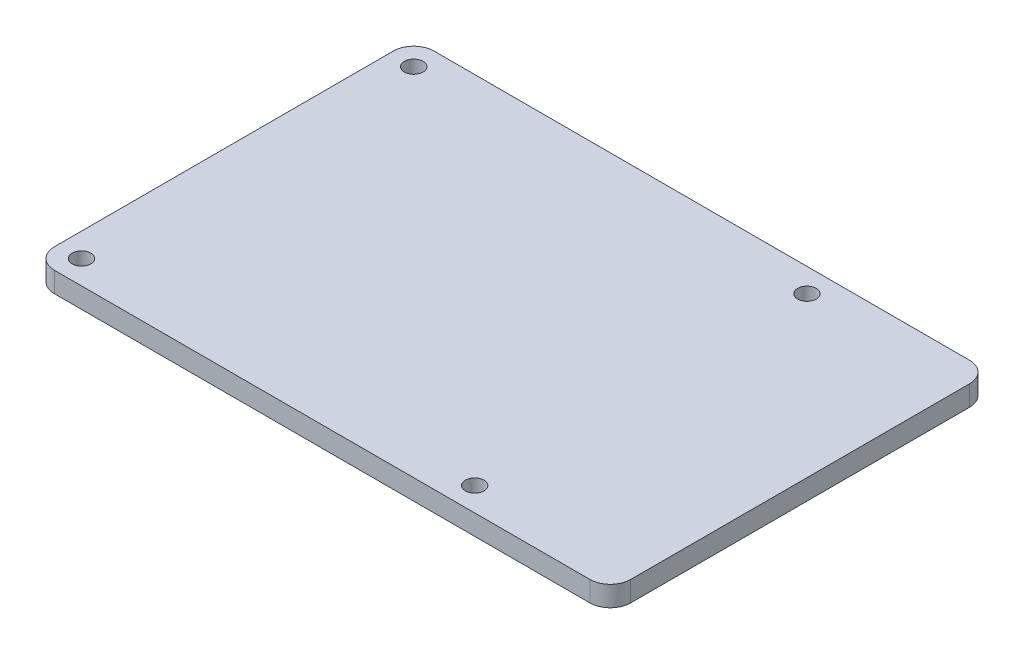
SolidWorks part; units mm, degrees
ref_plane "Front Plane" through (0, 0, 0) normal (0, 0, 1) x (1, 0, 0)
ref_plane "Top Plane" through (0, 0, 0) normal (0, 1, 0) x (1, 0, 0)
ref_plane "Right Plane" through (0, 0, 0) normal (1, 0, 0) x (0, 0, -1)
sketch "Sketch1" plane through (0, 0, 0) normal (0, 1, 0) x (1, 0, 0)
  line L0 (0, 28) -> (85, 28) construction
  line L1 (3, 0) -> (82, 0)
  line L2 (0, 3) -> (0, 53)
  line L3 (3, 56) -> (82, 56)
  line L4 (85, 3) -> (85, 53)
  arc A0 (82, 0) -> (85, 3) centre (82, 3) ccw
  arc A1 (82, 56) -> (85, 53) centre (82, 53) cw
  arc A2 (0, 53) -> (3, 56) centre (3, 53) cw
  arc A3 (3, 0) -> (0, 3) centre (3, 3) cw
  circle A4 centre (3.5, 52.5) radius 1.375
  circle A5 centre (3.5, 3.5) radius 1.375
  circle A6 centre (61.5, 3.5) radius 1.375
  circle A7 centre (61.5, 52.5) radius 1.375
  point P13 (0, 0)
  dimension "D3" = 3
  dimension "D4" = 2.75
  dimension "D5" = 2.75
  dimension "D6" = 2.75
  dimension "D7" = 2.75
  dimension "D1" = 56
  dimension "D2" = 85
  dimension "D8" = 3.5
  dimension "D9" = 24.5
  dimension "D10" = 49
  dimension "D11" = 58
extrude "Boss-Extrude1" add sketch "Sketch1" along normal blind 3
